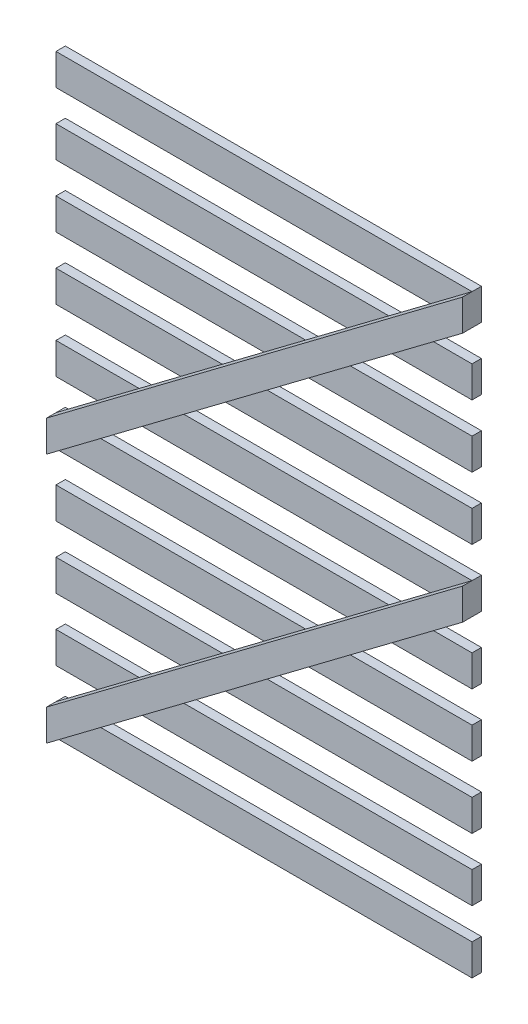
SolidWorks part; units mm, degrees
material "Mahogany"
ref_plane "Front Plane" through (0, 0, 0) normal (0, 0, 1) x (1, 0, 0)
ref_plane "Top Plane" through (0, 0, 0) normal (0, 1, 0) x (1, 0, 0)
ref_plane "Right Plane" through (0, 0, 0) normal (1, 0, 0) x (0, 0, -1)
sketch "Sketch1" plane through (0, 0, 0) normal (0, 0, 1) x (1, 0, 0)
  line L0 (0, -250) -> (0, -350)
  line L1 (0, 0) -> (1330, 0)
  line L2 (0, 0) -> (0, -2000)
  line L3 (0, -2000) -> (1330, -2000)
  line L4 (1330, 0) -> (1330, -2000)
  line L5 (0, -50) -> (1330, -50)
  line L6 (0, -50) -> (0, -150)
  line L7 (0, -150) -> (1330, -150)
  line L8 (1330, -50) -> (1330, -150)
  line L9 (0, -250) -> (1330, -250)
  line L10 (1330, -250) -> (1330, -350)
  line L11 (0, -350) -> (1330, -350)
  line L12 (0, -450) -> (0, -550)
  line L13 (0, -450) -> (1330, -450)
  line L14 (1330, -450) -> (1330, -550)
  line L15 (0, -550) -> (1330, -550)
  line L16 (0, -650) -> (0, -750)
  line L17 (0, -650) -> (1330, -650)
  line L18 (1330, -650) -> (1330, -750)
  line L19 (0, -750) -> (1330, -750)
  line L20 (0, -850) -> (0, -950)
  line L21 (0, -850) -> (1330, -850)
  line L22 (1330, -850) -> (1330, -950)
  line L23 (0, -950) -> (1330, -950)
  line L24 (0, -1050) -> (0, -1150)
  line L25 (0, -1050) -> (1330, -1050)
  line L26 (1330, -1050) -> (1330, -1150)
  line L27 (0, -1150) -> (1330, -1150)
  line L28 (0, -1250) -> (0, -1350)
  line L29 (0, -1250) -> (1330, -1250)
  line L30 (1330, -1250) -> (1330, -1350)
  line L31 (0, -1350) -> (1330, -1350)
  line L32 (0, -1450) -> (0, -1550)
  line L33 (0, -1450) -> (1330, -1450)
  line L34 (1330, -1450) -> (1330, -1550)
  line L35 (0, -1550) -> (1330, -1550)
  line L36 (0, -1650) -> (0, -1750)
  line L37 (0, -1650) -> (1330, -1650)
  line L38 (1330, -1650) -> (1330, -1750)
  line L39 (0, -1750) -> (1330, -1750)
  line L40 (0, -1850) -> (0, -1950)
  line L41 (0, -1850) -> (1330, -1850)
  line L42 (1330, -1850) -> (1330, -1950)
  line L43 (0, -1950) -> (1330, -1950)
  dimension "D1" = 2000
  dimension "D2" = 1330
  dimension "D3" = 100
  dimension "D4" = 50
  dimension "D5" = 10
extrude "Boss-Extrude1" add sketch "Sketch1" along normal blind 30 contours L2 L15 L4 L13 | L2 L19 L4 L17 | L2 L23 L4 L21 | L2 L27 L4 L25 | L2 L31 L4 L29 | L2 L43 L4 L41 | L5 L8 L7 L6 | L9 L10 L11 L0 | L33 L34 L35 L32 | L37 L38 L39 L36
sketch "Sketch2" plane through (0, 0, 30) normal (0, 0, 1) x (1, 0, 0)
  line L0 (1330, -50) -> (0, -1050)
  line L1 (1330, -50) -> (1330, -150)
  line L2 (0, -1050) -> (0, -1150)
  line L3 (1330, -150) -> (0, -1150)
  line L4 (1330, -850) -> (0, -1850)
  line L5 (1330, -850) -> (1330, -950)
  line L6 (0, -1850) -> (0, -1950)
  line L7 (1330, -950) -> (0, -1950)
extrude "Boss-Extrude2" add sketch "Sketch2" along normal blind 30
